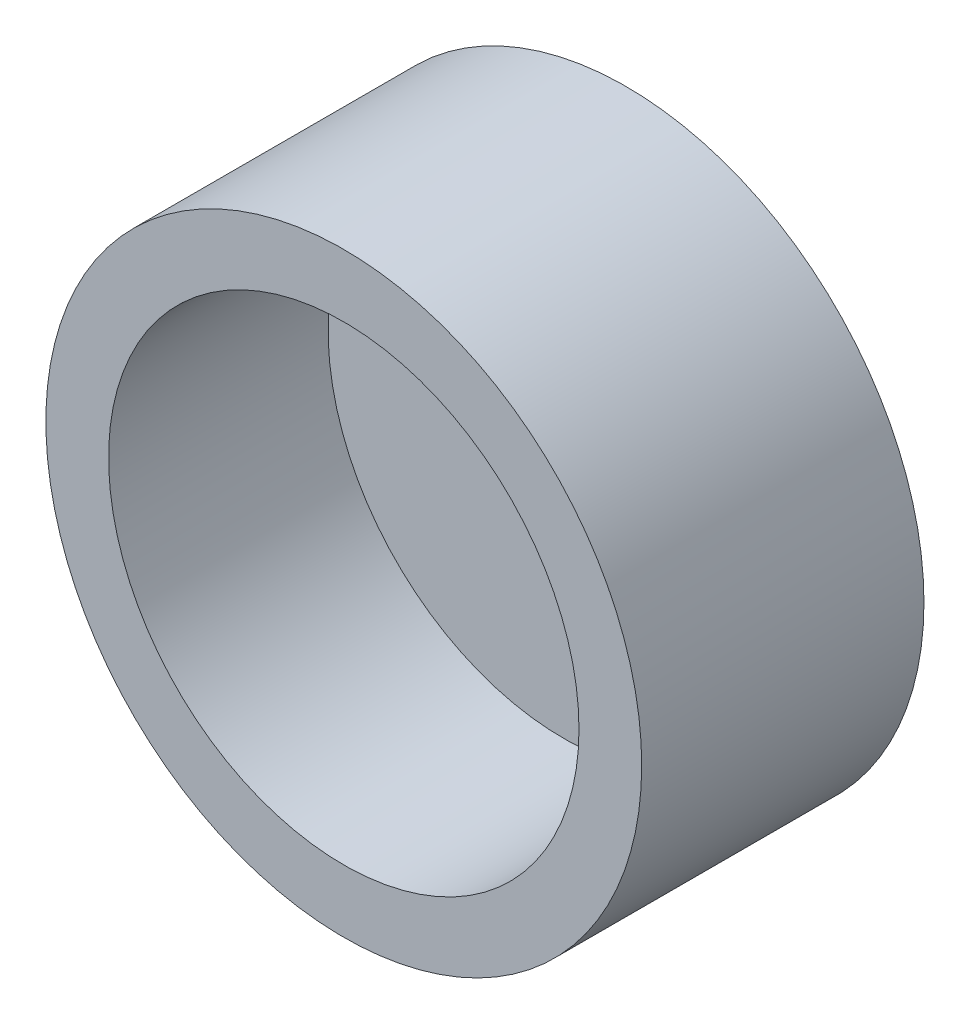
SolidWorks part; units mm, degrees
material "CA"
ref_plane "Front Plane" through (0, 0, 0) normal (0, 0, 1) x (1, 0, 0)
ref_plane "Top Plane" through (0, 0, 0) normal (0, 1, 0) x (1, 0, 0)
ref_plane "Right Plane" through (0, 0, 0) normal (1, 0, 0) x (0, 0, -1)
sketch "Sketch1" plane through (0, 0, 0) normal (0, 0, 1) x (1, 0, 0)
  circle A0 centre (0, 0) radius 9.5
  dimension "D1" = 19
extrude "Boss-Extrude1" add sketch "Sketch1" along normal blind 9
sketch "Sketch2" plane through (0, 0, 9) normal (0, 0, 1) x (1, 0, 0)
  circle A0 centre (0, 0) radius 7.5
  dimension "D1" = 15
extrude "Cut-Extrude1" cut sketch "Sketch2" against normal blind 7
